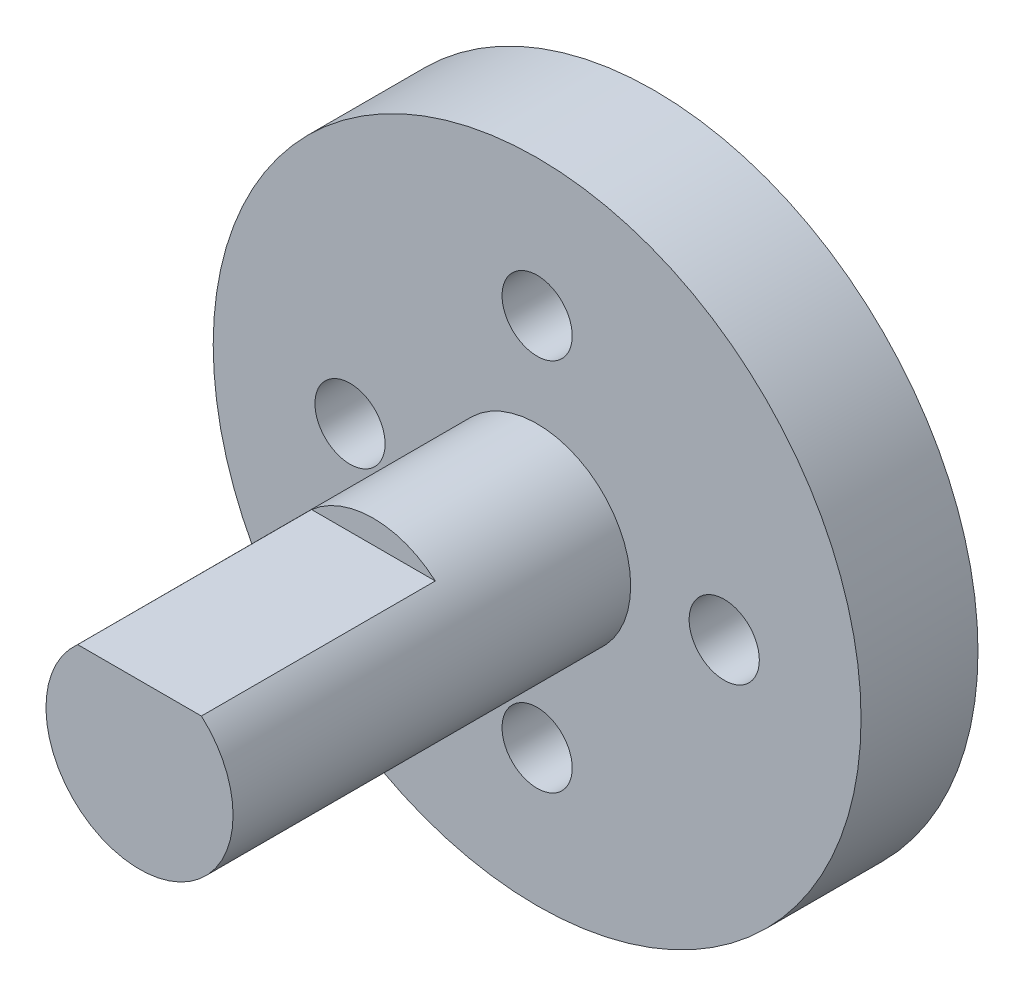
SolidWorks part; units mm, degrees
ref_plane "Front Plane" through (0, 0, 0) normal (0, 0, 1) x (1, 0, 0)
ref_plane "Top Plane" through (0, 0, 0) normal (0, 1, 0) x (1, 0, 0)
ref_plane "Right Plane" through (0, 0, 0) normal (1, 0, 0) x (0, 0, -1)
sketch "Sketch2" plane through (0, 0, 0) normal (0, 0, 1) x (1, 0, 0)
  circle A0 centre (0, 0) radius 13.85
  circle A1 centre (0, 0) radius 4
  circle A9 centre (0, 8) radius 1.5
  circle A11 centre (-8, 0) radius 1.5
  circle A12 centre (8, 0) radius 1.5
  circle A13 centre (0, -8) radius 1.5
extrude "Boss-Extrude1" add sketch "Sketch2" along normal blind 5
sketch "Sketch3" plane through (0, 0, 5) normal (0, 0, 1) x (1, 0, 0)
  circle A0 centre (0, 0) radius 4
extrude "Boss-Extrude2" add sketch "Sketch3" along normal blind 17 and the other way blind 5
sketch "Sketch4" plane through (0, 0, 22) normal (0, 0, 1) x (1, 0, 0)
  line L1 (-2.6458, 3) -> (2.6458, 3)
  arc A0 (2.6458, 3) -> (-2.6458, 3) centre (0, 0) ccw
extrude "Cut-Extrude1" cut sketch "Sketch4" against normal blind 10
